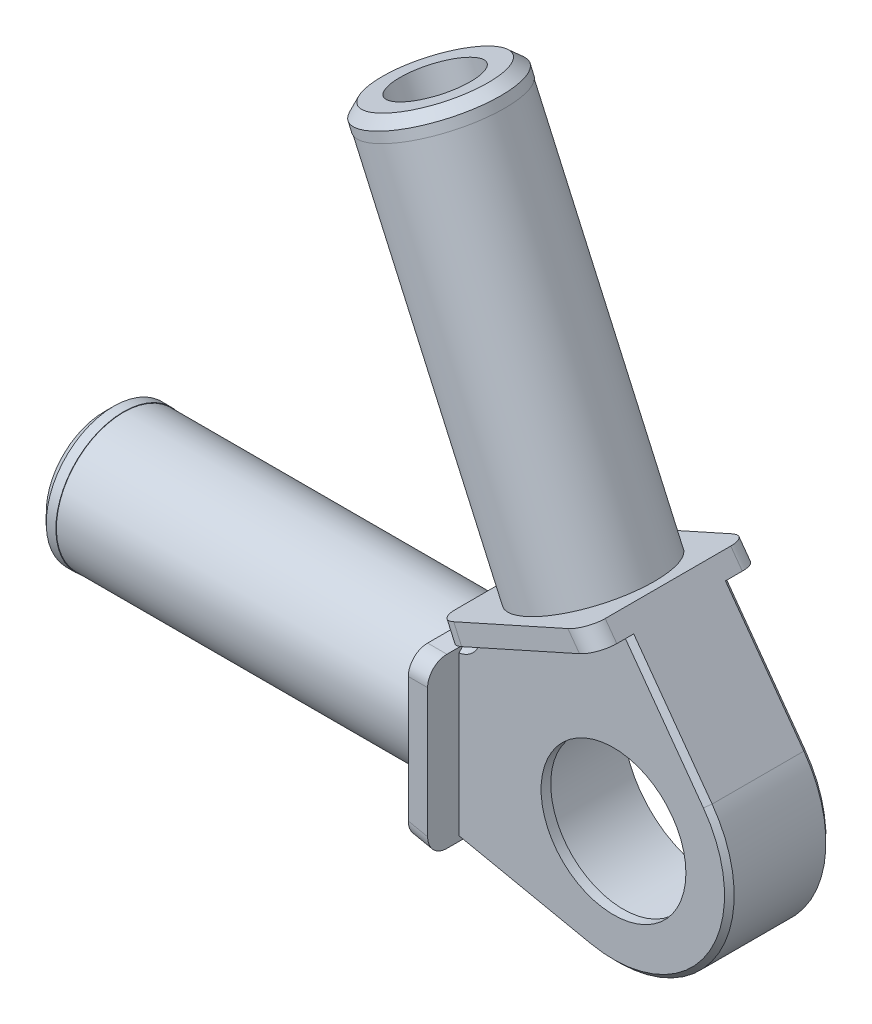
SolidWorks part; units mm, degrees
material "7075-T6 (SN)"
ref_plane "Płaszczyzna XY" through (0, 0, 0) normal (0, 0, 1) x (1, 0, 0)
ref_plane "Płaszczyzna XZ" through (0, 0, 0) normal (0, 1, 0) x (1, 0, 0)
ref_plane "Płaszczyzna YZ" through (0, 0, 0) normal (1, 0, 0) x (0, 0, -1)
sketch "Szkic1" plane through (0, 0, 0) normal (0, 0, 1) x (1, 0, 0)
  line L0 (0, 0) -> (-69.9038, 0) construction
  line L1 (0, 0) -> (-34.0939, 76.0717) construction
  line L2 (-18, -8.5) -> (-2.453, -11.7466)
  line L3 (-18, -8.5) -> (-18, 8.5)
  line L4 (-15.1183, 12.9494) -> (0.3949, 19.9021)
  line L5 (0.3949, 19.9021) -> (9.716, 7.0426)
  line L6 (-18, 8.5) -> (-16, 8.5)
  line L7 (-15.1183, 12.9494) -> (-14.3003, 11.1243)
  circle A0 centre (0, 0) radius 9.5
  arc A1 (-2.453, -11.7466) -> (9.716, 7.0426) centre (0, 0) ccw
  arc A5 (-14.3003, 11.1243) -> (-16, 8.5) centre (-16.4623, 10.662) cw
  dimension "D1" = 2.5
  dimension "D2" = 19
  dimension "D10" = 2
  dimension "D12" = 2.2109
  dimension "D3" = 65.859
  dimension "D4" = 8.5
  dimension "D5" = 8.5
  dimension "D6" = 18
  dimension "D7" = 18
  dimension "D8" = 8.5
  dimension "D9" = 8.5
  dimension "D11" = 2
extrude "Dodanie-wyciągnięcie1" add sketch "Szkic1" along normal blind 10.5
ref_plane "Płaszczyzna1" through (0, 0, 5.25) normal (0, 0, 1) x (1, 0, 0)
sketch "Szkic2" plane through (0, 0, 5.25) normal (0, 0, 1) x (1, 0, 0)
  line L0 (0, 0) -> (-58, 0) construction
  line L1 (-18, 8.5) -> (-18, -8.5) construction
  line L2 (-58, 0) -> (-58, -7)
  line L3 (-58, -7) -> (-56, -7)
  line L4 (-58, 0) -> (-18, 0)
  line L5 (-18, 0) -> (-18, -6.95)
  line L6 (-56, -7) -> (-56, -6.95)
  line L7 (-56, -6.95) -> (-18, -6.95)
  dimension "D1" = 40
  dimension "D2" = 7
  dimension "D3" = 2
  dimension "D4" = 6.95
  dimension "D5" = 0
revolve "Obrót1" add sketch "Szkic2" angle 360 about L0
sketch "Szkic3" plane through (0, 0, 5.25) normal (0, 0, 1) x (1, 0, 0)
  line L0 (0, 0) -> (-23.7211, 52.9274) construction
  line L1 (0.3949, 19.9021) -> (-15.1183, 12.9494) construction
  line L2 (-23.7211, 52.9274) -> (-17.3333, 55.7903)
  line L3 (-17.3333, 55.7903) -> (-16.5153, 53.9652)
  line L4 (-1.0196, 19.2682) -> (-7.3617, 16.4257)
  line L5 (-7.3617, 16.4257) -> (-23.7211, 52.9274)
  line L6 (-16.5153, 53.9652) -> (-16.561, 53.9448)
  line L7 (-16.561, 53.9448) -> (-1.0196, 19.2682)
  line L8 (0.3949, 19.9021) -> (-15.1183, 12.9494) construction
  dimension "D1" = 40
  dimension "D2" = 2
  dimension "D3" = 7
  dimension "D4" = 6.95
  dimension "D5" = 38
  dimension "D6" = 90
revolve "Obrót2" add sketch "Szkic3" angle 360 about L0
sketch "Szkic4" plane through (0, 0, 10.5) normal (0, 0, 1) x (1, 0, 0)
  circle A0 centre (0, 0) radius 9.5
  circle A1 centre (0, 0) radius 7.5
  dimension "D1" = 2
  dimension "D2" = 19
extrude "Dodanie-wyciągnięcie2" add sketch "Szkic4" against normal blind 1
sketch "Szkic8" plane through (0, 0, 10.5) normal (0, 0, 1) x (1, 0, 0)
  line L1 (-18, 8.5) -> (-18, -8.5)
  line L2 (-18, -8.5) -> (-16, -8.9177)
  line L3 (-18, -8.5) -> (-2.453, -11.7466) construction
  line L7 (9.716, 7.0426) -> (0.3949, 19.9021) construction
  line L8 (1.594, 18.2478) -> (0.3949, 19.9021)
  line L9 (0.3949, 19.9021) -> (-15.1183, 12.9494)
  line L18 (-18, 8.5) -> (-16, 8.5)
  line L19 (-16, 8.5) -> (-16, -8.9177)
  line L20 (-15.1183, 12.9494) -> (-14.3003, 11.1243)
  line L21 (-14.3003, 11.1243) -> (1.594, 18.2478)
extrude "Dodanie-wyciągnięcie5" add sketch "Szkic8" along normal blind 3.25 and the other way blind 13.75
fillet "Zaokrąglenie1" radius 2 8 edges at (0.9944, 19.075, 13.75) (0.9944, 19.075, -3.25) (-17, -8.7088, -3.25) (-17, -8.7088, 13.75) (-17, 8.5, 13.75) (-14.7093, 12.0368, 13.75) (-14.7093, 12.0368, -3.25) (-17, 8.5, -3.25)
chamfer "Sfazowanie1" distance 0.5 angle 45 8 edges at (-9.2265, -10.3321, 10.5) (10.0721, -6.5233, 10.5) (5.655, 12.6452, 10.5) (-9.2265, -10.3321, 0) (10.0721, -6.5233, 0) (5.655, 12.6452, 0) (-14.6067, 9.4601, 0) (-14.6067, 9.4601, 10.5)
fillet "Zaokrąglenie2" radius 0.5 1 edges at (9.5, 0, 9.5)
chamfer "Sfazowanie2" distance 1 angle 45 2 edges at (-58, 7, 5.25) (-17.3333, 55.7903, 5.25)
hole_wizard "Otwory ustalające Ø8.0mm4" positions "Szkic 3D1" profile "Szkic9" hole size "Ø8.0" standard "ISO"
sketch3d "Szkic 3D1"
  line L0 (-23.3121, 52.0149, 5.25) -> (-23.7211, 52.9274, 5.25) construction
  point P0 (-23.7211, 52.9274, 5.25)
sketch "Szkic9" plane through (-23.7211, 52.9274, 5.25) normal (0, 0, 1) x (-0.9125, -0.409, 0)
  line L0 (0, 0) -> (0, 42.4034)
  line L1 (0, 42.4034) -> (4, 40)
  line L2 (4, 40) -> (4, 0)
  line L5 (4, 0) -> (0, 0)
  line L10 (0, 42.4034) -> (-4, 40) construction
  line L11 (0, -6.35) -> (0, 107.95) construction
  dimension "Średnica otworu" = 8
  dimension "Głębokość otworu" = 40
  dimension "Kąt wiertła" = 118
hole_wizard "Otwory ustalające Ø8.0mm2" positions "Szkic 3D2" profile "Szkic10" hole size "Ø8.0" standard "ISO"
sketch3d "Szkic 3D2"
  line L0 (-57, 0, 5.25) -> (-58, 0, 5.25) construction
  point P0 (-58, 0, 5.25)
sketch "Szkic10" plane through (-58, 0, 5.25) normal (0, 1, 0) x (0, 0, 1)
  line L0 (0, 0) -> (0, 42.4034)
  line L1 (0, 42.4034) -> (4, 40)
  line L2 (4, 40) -> (4, 0)
  line L5 (4, 0) -> (0, 0)
  line L10 (0, 42.4034) -> (-4, 40) construction
  line L11 (0, -6.35) -> (0, 107.95) construction
  dimension "Średnica otworu" = 8
  dimension "Głębokość otworu" = 40
  dimension "Kąt wiertła" = 118
